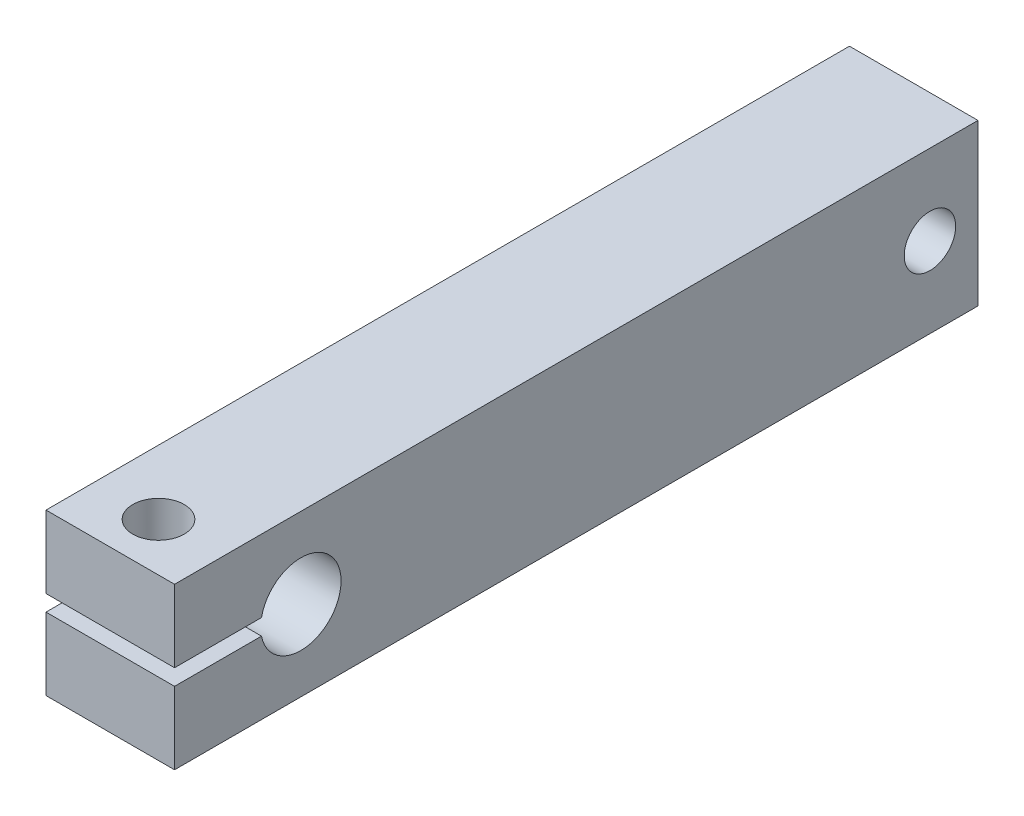
SolidWorks part; units mm, degrees
ref_plane "前视基准面" through (0, 0, 0) normal (0, 0, 1) x (1, 0, 0)
ref_plane "上视基准面" through (0, 0, 0) normal (0, 1, 0) x (1, 0, 0)
ref_plane "右视基准面" through (0, 0, 0) normal (1, 0, 0) x (0, 0, -1)
sketch "草图1" plane through (0, 0, 0) normal (0, 0, 1) x (1, 0, 0)
  line L1 (0, 0) -> (8, 0)
  line L2 (0, 0) -> (0, 10)
  line L3 (0, 10) -> (8, 10)
  line L4 (8, 0) -> (8, 10)
extrude "凸台-拉伸1" add sketch "草图1" along normal blind 40
sketch "草图3" plane through (0, 0, 0) normal (0, -1, 0) x (1, 0, 0)
  circle A0 centre (4, 37) radius 1.6
sketch "草图5" plane through (0, 0, 0) normal (0, 0, -1) x (-1, 0, 0)
  line L1 (-8, 10) -> (0, 10)
  line L2 (-8, 10) -> (-8, 0)
  line L3 (-8, 0) -> (0, 0)
  line L4 (0, 10) -> (0, 0)
extrude "凸台-拉伸2" add sketch "草图5" along normal blind 10
sketch "草图7" plane through (8, 0, 0) normal (1, 0, 0) x (0, 0, -1)
  circle A0 centre (7.0095, 5) radius 1.6
extrude "切除-拉伸4" cut sketch "草图7" against normal through all
sketch "草图10" plane through (0, 0, 0) normal (-1, 0, 0) x (0, 0, 1)
  line L0 (40, 5) -> (40, 5.5)
  line L1 (40, 10) -> (40, 0) construction
  line L2 (40, 5.5) -> (34.59, 5.5)
  line L4 (34.59, 4.5) -> (40, 4.5)
  line L5 (40, 4.5) -> (40, 5)
  arc A0 (34.59, 5.5) -> (34.59, 4.5) centre (32.14, 5) ccw
extrude "切除-拉伸6" cut sketch "草图10" against normal through all
extrude "切除-拉伸7" cut sketch "草图3" against normal through all
